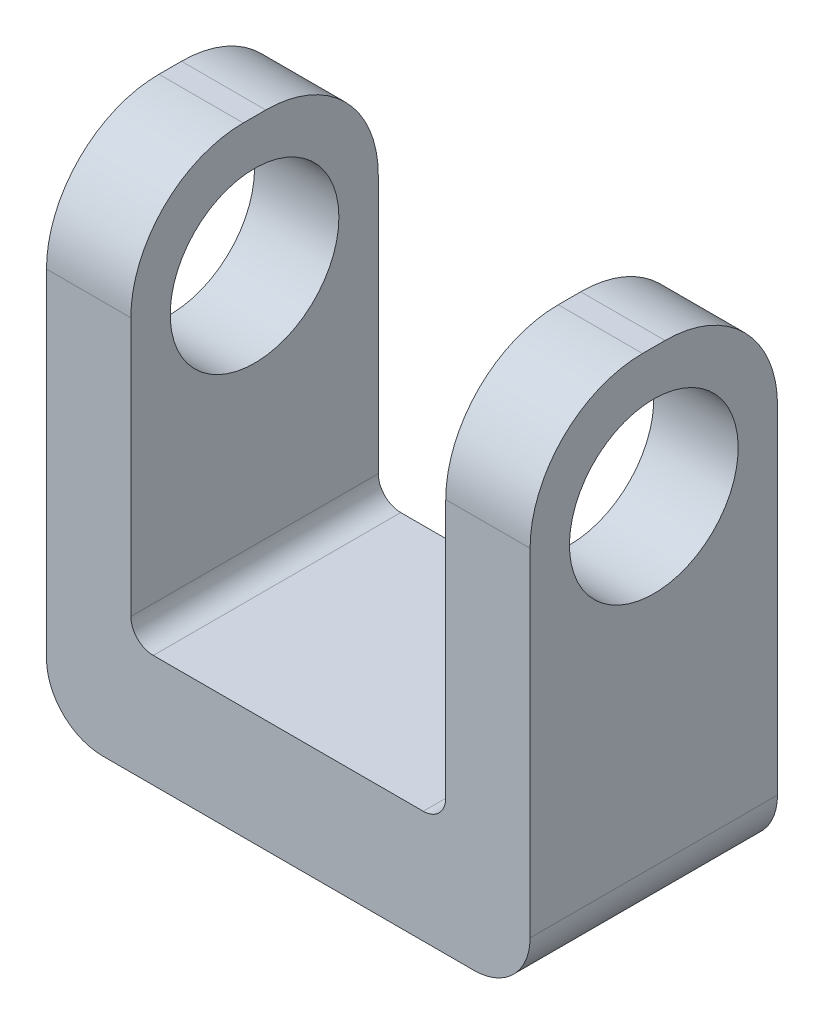
SolidWorks part; units mm, degrees
material "1.0503 (C45)"
ref_plane "Płaszczyzna przednia" through (0, 0, 0) normal (0, 0, 1) x (1, 0, 0)
ref_plane "Płaszczyzna górna" through (0, 0, 0) normal (0, 1, 0) x (1, 0, 0)
ref_plane "Płaszczyzna prawa" through (0, 0, 0) normal (1, 0, 0) x (0, 0, -1)
sketch "Szkic1" plane through (0, 0, 0) normal (0, 0, 1) x (1, 0, 0)
  line L1 (-21.5, 0) -> (21.5, 0)
  line L2 (-21.5, 0) -> (-21.5, 45)
  line L3 (-21.5, 45) -> (21.5, 45)
  line L4 (21.5, 0) -> (21.5, 45)
  point P5 (0, 0)
  dimension "D1" = 43
  dimension "D2" = 45
extrude "Dodanie-wyciągnięcie1" add sketch "Szkic1" along normal blind 22
sketch "Szkic3" plane through (0, 0, 0) normal (0, 0, 1) x (1, 0, 0)
  line L0 (21.5, 45) -> (-21.5, 45) construction
  line L1 (14, 10) -> (-14, 10)
  line L2 (14, 10) -> (14, 45)
  line L3 (14, 45) -> (-14, 45)
  line L4 (-14, 10) -> (-14, 45)
  point P6 (0, 45)
  point P7 (0, 45)
  dimension "D1" = 28
  dimension "D2" = 35
extrude "Wytnij-wyciągnięcie1" cut sketch "Szkic3" along normal blind 63
sketch "Szkic4" plane through (21.5, 0, 0) normal (1, 0, 0) x (0, 0, -1)
  line L0 (-11, 45) -> (-11, 0) construction
  line L1 (-22, 45) -> (0, 45) construction
  line L2 (-22, 0) -> (0, 0) construction
  circle A0 centre (-11, 33.5) radius 7.5
  dimension "D1" = 15
  dimension "D2" = 11.5
extrude "Wytnij-wyciągnięcie2" cut sketch "Szkic4" against normal blind 63
fillet "Zaokrąglenie1" radius 10 4 edges at (17.75, 45, 22) (-17.75, 45, 22) (-17.75, 45, 0) (17.75, 45, 0)
fillet "Zaokrąglenie2" radius 2 2 edges at (14, 10, 11) (-14, 10, 11)
fillet "Zaokrąglenie3" radius 5 2 edges at (-21.5, 0, 11) (21.5, 0, 11)
sketch "Szkic5" plane through (0, 0, 0) normal (0, -1, 0) x (-1, 0, 0)
  line L0 (16.5, -11) -> (-16.5, -11) construction
  line L1 (16.5, -22) -> (16.5, 0) construction
  line L2 (-16.5, 0) -> (-16.5, -22) construction
  line L3 (0, -22) -> (0, 0) construction
  line L4 (16.5, -22) -> (-16.5, -22) construction
  circle A0 centre (0, -11) radius 4.9254 construction
